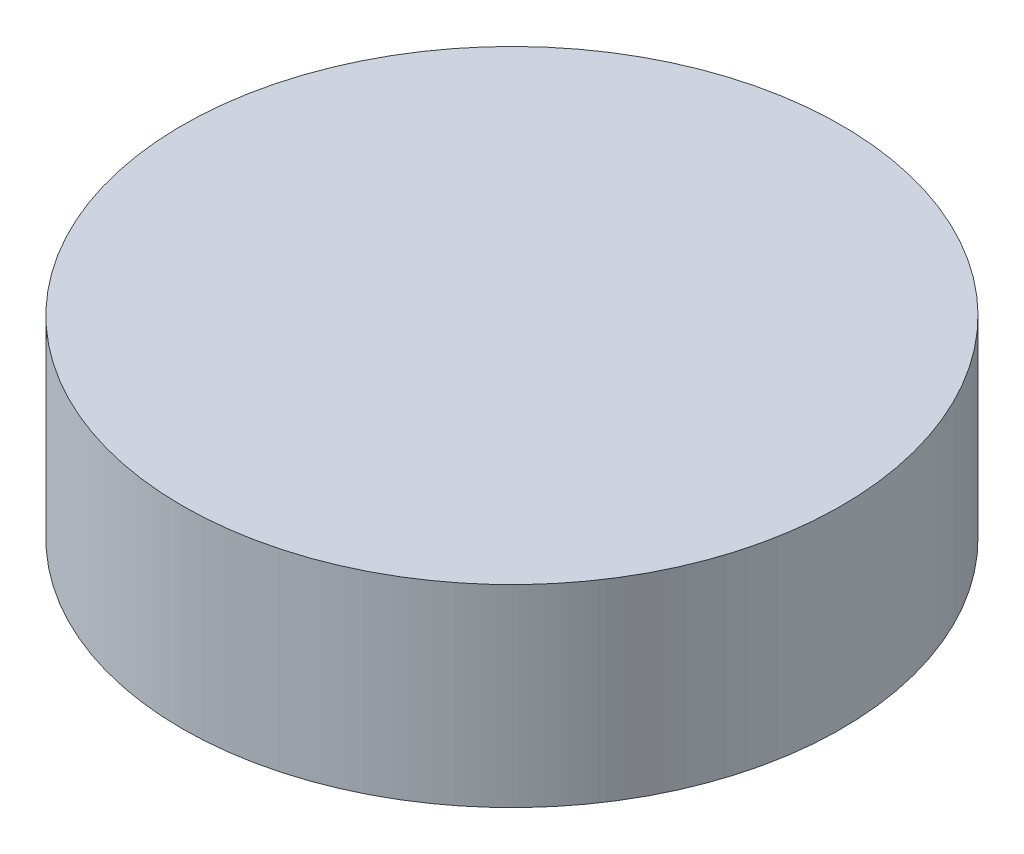
SolidWorks part; units mm, degrees
ref_plane "Front Plane" through (0, 0, 0) normal (0, 0, 1) x (1, 0, 0)
ref_plane "Top Plane" through (0, 0, 0) normal (0, 1, 0) x (1, 0, 0)
ref_plane "Right Plane" through (0, 0, 0) normal (1, 0, 0) x (0, 0, -1)
sketch "Sketch2" plane through (0, 0, 0) normal (0, 1, 0) x (1, 0, 0)
  circle A0 centre (0, 0) radius 5
extrude "Boss-Extrude1" add sketch "Sketch2" along normal blind 2.93
